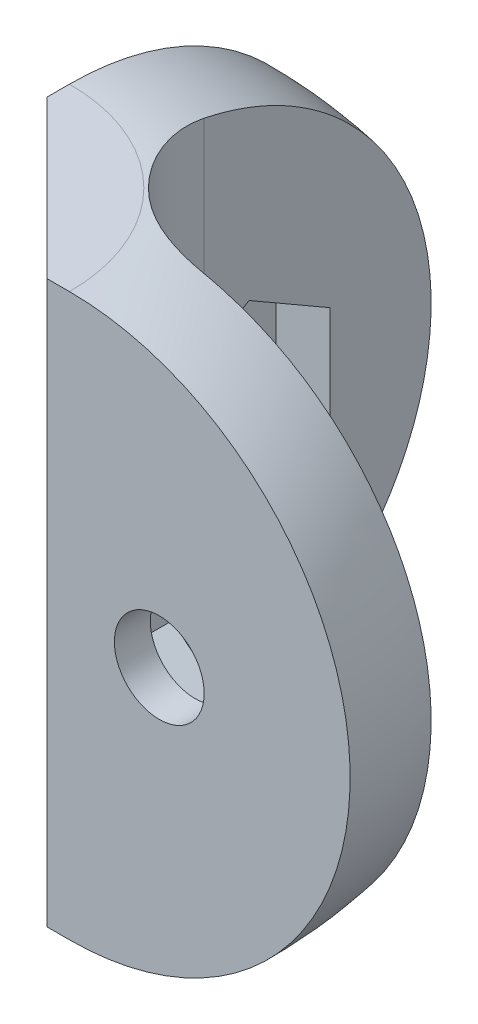
SolidWorks part; units mm, degrees
ref_plane "Front Plane" through (0, 0, 0) normal (0, 0, 1) x (1, 0, 0)
ref_plane "Top Plane" through (0, 0, 0) normal (0, 1, 0) x (1, 0, 0)
ref_plane "Right Plane" through (0, 0, 0) normal (1, 0, 0) x (0, 0, -1)
sketch "Sketch1" plane through (0, 0, 0) normal (0, 1, 0) x (1, 0, 0)
  line L0 (0, 0) -> (0, 25)
  line L1 (0, 0) -> (25, 0)
  line L2 (0, 25) -> (4, 25)
  line L3 (25, 0) -> (25, 4)
  line L4 (25, 4) -> (10, 4)
  line L5 (4, 10) -> (4, 25)
  arc A0 (10, 4) -> (4, 10) centre (10, 10) cw
  point P3 (3.485, 3.485)
  point P8 (0, 0)
  dimension "D3" = 6
  dimension "D1" = 25
  dimension "D2" = 4
extrude "Boss-Extrude1" add sketch "Sketch1" along normal blind 25
sketch "Sketch2" plane through (0, 0, 0) normal (0, 0, 1) x (1, 0, 0)
  line L1 (0, 12.5) -> (25, 12.5) construction
  line L2 (0, 25) -> (0, 0) construction
  line L3 (25, 25) -> (25, 0) construction
  line L4 (0, 0) -> (25, 0) construction
  line L5 (8, 0) -> (0, 0)
  line L6 (8, 25) -> (0, 25)
  line L8 (0, 25) -> (25, 25) construction
  line L9 (0, 25) -> (0, 28.5811)
  line L10 (0, 28.5811) -> (27.824, 28.5811)
  line L11 (27.824, 28.5811) -> (27.824, -0.9473)
  line L12 (27.824, -0.9473) -> (0, -0.9473)
  line L13 (0, -0.9473) -> (0, 0)
  arc A2 (8, 25) -> (8, 0) centre (8, 12.5) cw
  point P23 (4.8768, 25)
  dimension "D1" = 12.5
  dimension "D2" = 8
revolve "Cut-Revolve2" cut sketch "Sketch2" angle 360 about L9
sketch "Sketch3" plane through (0, 0, 0) normal (0, 0, 1) x (1, 0, 0)
  line L0 (0, 25) -> (0, 0) construction
  line L1 (0, 12.5) -> (12, 12.5) construction
  circle A0 centre (12, 12.5) radius 2
  point P6 (0, 0)
  dimension "D1" = 4
  dimension "D2" = 12
extrude "Cut-Extrude1" cut sketch "Sketch3" against normal through all
sketch "Sketch4" plane through (0, 0, 0) normal (-1, 0, 0) x (0, 0, 1)
  line L0 (0, 12.5) -> (-12, 12.5) construction
  line L1 (0, 25) -> (0, 0) construction
  circle A0 centre (-12, 12.5) radius 2
  dimension "D1" = 4
  dimension "D2" = 12
extrude "Cut-Extrude2" cut sketch "Sketch4" against normal through all
sketch "Sketch5" plane through (0, 0, 0) normal (-1, 0, 0) x (0, 0, 1)
  line L1 (-8.4, 14.5785) -> (-12, 16.6569)
  line L2 (-12, 16.6569) -> (-15.6, 14.5785)
  line L3 (-15.6, 14.5785) -> (-15.6, 10.4215)
  line L4 (-15.6, 10.4215) -> (-12, 8.3431)
  line L5 (-12, 8.3431) -> (-8.4, 10.4215)
  line L6 (-8.4, 10.4215) -> (-8.4, 14.5785)
  circle A0 centre (-12, 12.5) radius 3.6 construction
  dimension "D1" = 7.2
extrude "Cut-Extrude3" cut sketch "Sketch5" against normal through all from offset 1.6 offset against normal yes
sketch "Sketch6" plane through (0, 0, 0) normal (0, 0, 1) x (1, 0, 0)
  line L1 (12, 8.3431) -> (15.6, 10.4215)
  line L2 (15.6, 10.4215) -> (15.6, 14.5785)
  line L3 (15.6, 14.5785) -> (12, 16.6569)
  line L4 (12, 16.6569) -> (8.4, 14.5785)
  line L5 (8.4, 14.5785) -> (8.4, 10.4215)
  line L6 (8.4, 10.4215) -> (12, 8.3431)
  circle A0 centre (12, 12.5) radius 3.6 construction
  dimension "D1" = 7.2
extrude "Cut-Extrude4" cut sketch "Sketch6" against normal through all from offset 1.6 offset against normal yes
chamfer "Chamfer1" distance 7 angle 45 1 edges at (0, 12.5, 0)
